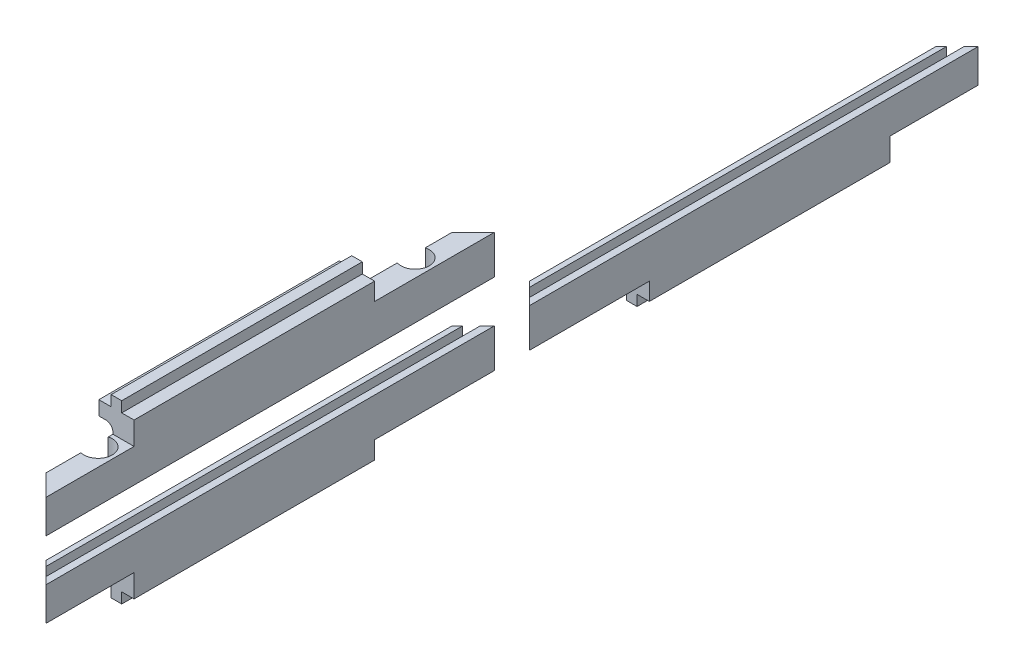
SolidWorks part; units mm, degrees
ref_plane "Front Plane" through (0, 0, 0) normal (0, 0, 1) x (1, 0, 0)
ref_plane "Top Plane" through (0, 0, 0) normal (0, 1, 0) x (1, 0, 0)
ref_plane "Right Plane" through (0, 0, 0) normal (1, 0, 0) x (0, 0, -1)
sketch "Sketch1" plane through (0, 0, 0) normal (0, 0, 1) x (1, 0, 0)
  line L0 (-5, -3) -> (-1.5, -3)
  line L1 (-1.5, -3) -> (-1.5, 0)
  line L2 (-1.5, 0) -> (1.5, 0)
  line L3 (1.5, 0) -> (1.5, -3)
  line L4 (1.5, -3) -> (5, -3)
  line L5 (5, -3) -> (5, -19)
  line L6 (5, -19) -> (3, -19)
  line L7 (3, -19) -> (3, -16)
  line L8 (3, -16) -> (0.5, -16)
  line L9 (0.5, -16) -> (0.5, -19)
  line L10 (0.5, -19) -> (-5, -19)
  line L11 (-5, -19) -> (-5, -3)
  point P12 (0, 0)
  point P13 (0, 0)
  point P14 (0, 0)
  point P15 (0, 0)
  point P17 (2.8849, -6.4186)
  point P18 (5, -13.5973)
  dimension "D1" = 3
  dimension "D2" = 3
  dimension "D3" = 10
  dimension "D4" = 2
  dimension "D5" = 2.5
  dimension "D6" = 16
  dimension "D7" = 3
extrude "Main" add sketch "Sketch1" along normal blind 127.3
sketch "Sketch2" plane through (0, 0, 0) normal (0, 1, 0) x (1, 0, 0)
  line L0 (5, -127.3) -> (-5, -117.3)
  line L1 (-5, -127.3) -> (-5, 0) construction
  line L2 (-5, -117.3) -> (-5, -127.3)
  line L3 (-5, -127.3) -> (5, -127.3)
  line L4 (5, 0) -> (-5, -10)
  line L5 (-5, -10) -> (-5, 0)
  line L6 (-5, 0) -> (5, 0)
  dimension "D1" = 45
  dimension "D2" = 45
extrude "CutDiagonale" cut sketch "Sketch2" against normal through all
sketch "Sketch3" plane through (0, 0, 0) normal (0, -1, 0) x (-1, 0, 0)
  line L0 (5, -117.3) -> (5, -10) construction
  line L5 (-5, -127.3) -> (-5, 0) construction
  line L7 (5, -10) -> (5, -34)
  line L8 (5, -34) -> (-5, -34)
  line L9 (-5, -34) -> (-5, 0)
  line L10 (-5, 0) -> (5, -10)
  dimension "D2" = 34
extrude "CutOtherPieceInRobotRight" cut sketch "Sketch3" along normal blind 8
sketch "Sketch6" plane through (0, 0, 0) normal (0, 1, 0) x (1, 0, 0)
  line L0 (5, -127.3) -> (5, -102.3)
  line L1 (5, -127.3) -> (5, -34) construction
  line L2 (5, -102.3) -> (-5, -102.3)
  line L3 (-5, -117.3) -> (-5, -34) construction
  line L4 (-5, -102.3) -> (-5, -117.3)
  line L5 (-5, -117.3) -> (5, -127.3)
  dimension "D1" = 25
extrude "CutOtherPieceInRobotLeft" cut sketch "Sketch6" against normal blind 9.5
sketch "Sketch4" plane through (0, -8, 0) normal (0, 1, 0) x (1, 0, 0)
  circle A0 centre (0, -17.5) radius 4
  circle A1 centre (0, -107.5) radius 4
  point P4 (0, 0)
  dimension "D1" = 8
  dimension "D2" = 90
  dimension "D3" = 17.5
  dimension "D4" = 19.8
extrude "ScrewHoles" cut sketch "Sketch4" against normal blind 8
sketch "Sketch5" plane through (0, -19, 0) normal (0, -1, 0) x (-1, 0, 0)
  line L0 (1, -121.3) -> (5, -117.3)
  line L1 (-0.5, -122.8) -> (5, -117.3) construction
  line L2 (5, -117.3) -> (5, -10)
  line L3 (5, -10) -> (1, -6)
  line L4 (5, -10) -> (-0.5, -4.5) construction
  line L5 (1, -6) -> (1, -121.3)
  dimension "D1" = 4
extrude "Cut-Extrude4" cut sketch "Sketch5" against normal blind 12
fillet "Fillet1" radius 2 1 edges at (-1, -7, 68.15)
ref_plane "Plane1" through (0, -25, 0) normal (0, 1, 0) x (1, 0, 0)
mirror "Mirror1" about plane through (0, -25, 0) normal (0, 1, 0) of bodies 105
ref_plane "Plane2" through (0, 0, -5) normal (0, 0, 1) x (1, 0, 0)
mirror "Mirror2" about plane through (0, 0, -5) normal (0, 0, 1) of bodies 107
